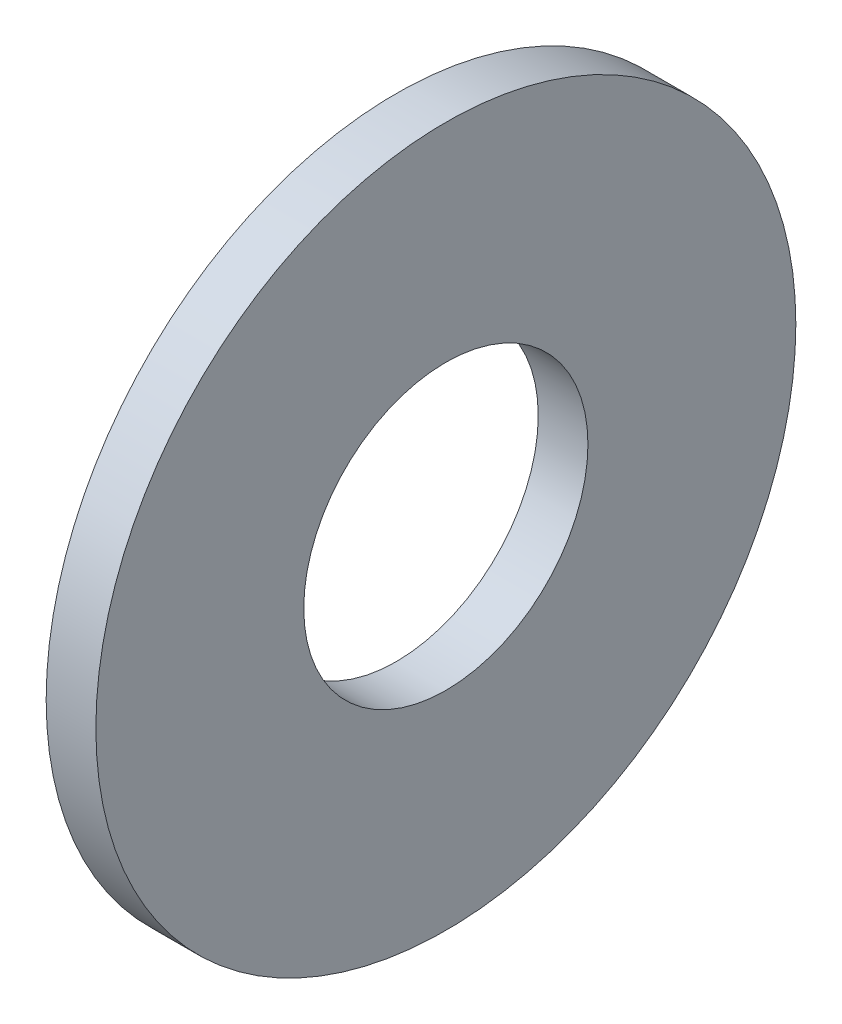
SolidWorks part; units mm, degrees
material "AISI 304"
ref_plane "Front Plane" through (0, 0, 0) normal (0, 0, 1) x (1, 0, 0)
ref_plane "Top Plane" through (0, 0, 0) normal (0, 1, 0) x (1, 0, 0)
ref_plane "Right Plane" through (0, 0, 0) normal (1, 0, 0) x (0, 0, -1)
sketch "Sketch1" plane through (0, 0, 0) normal (1, 0, 0) x (0, 0, -1)
  circle A0 centre (0, 0) radius 12.7
  circle A1 centre (0, 0) radius 5.1562
  dimension "OD" = 25.4
  dimension "ID" = 10.3124
extrude "Boss-Extrude1" add sketch "Sketch1" along normal blind 1.8034
